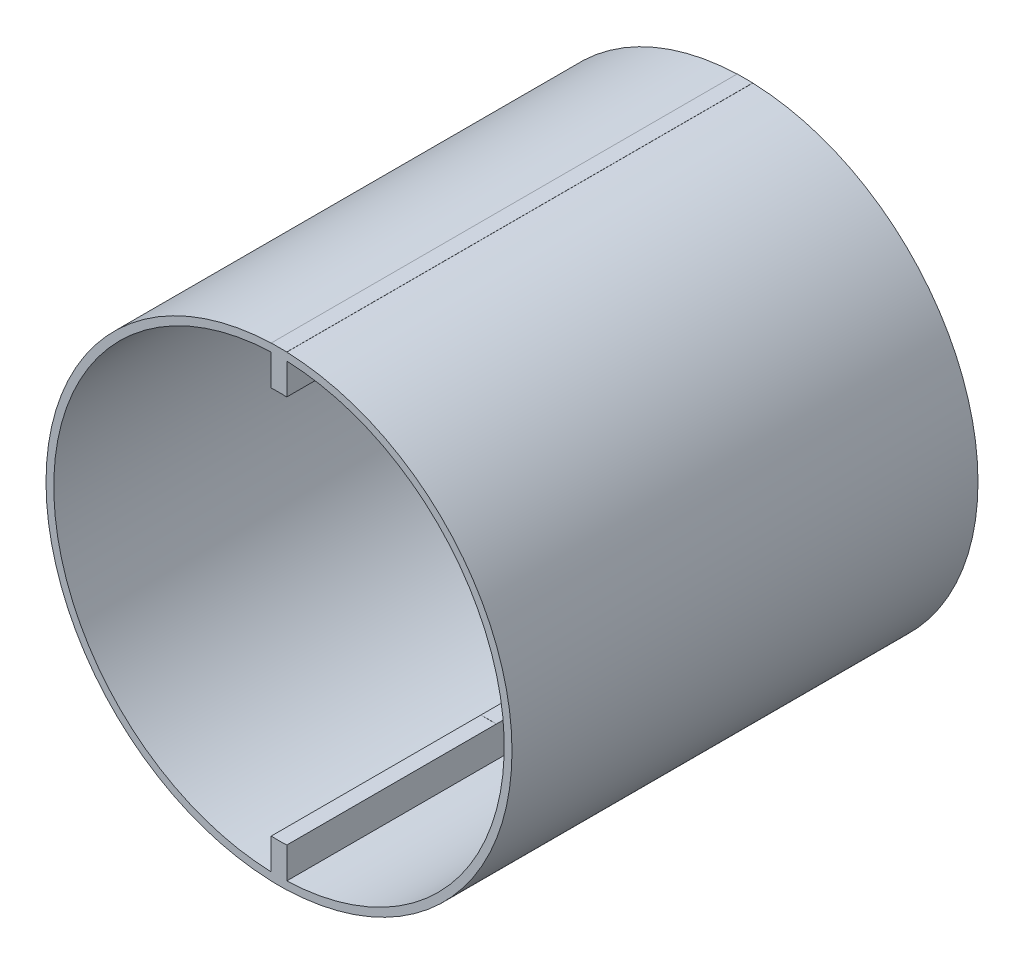
SolidWorks part; units mm, degrees
ref_plane "Plan de face" through (0, 0, 0) normal (0, 0, 1) x (1, 0, 0)
ref_plane "Plan de dessus" through (0, 0, 0) normal (0, 1, 0) x (1, 0, 0)
ref_plane "Plan de droite" through (0, 0, 0) normal (1, 0, 0) x (0, 0, -1)
sketch "Esquisse1" plane through (0, 0, 0) normal (0, 0, 1) x (1, 0, 0)
  line L0 (1, -15.0065) -> (1, -3.3541)
  line L1 (1, 30) -> (-1, 30)
  line L2 (-1, 30) -> (-1, 3.3541)
  line L3 (-1, -30) -> (1, -30)
  line L4 (1, -30) -> (1, -15.0065)
  line L5 (-1, -3.3541) -> (-1, -30)
  line L6 (1, 3.3541) -> (1, 30)
  arc A0 (-1, 3.3541) -> (-1, -3.3541) centre (0, 0) ccw
  arc A1 (1, -3.3541) -> (1, 3.3541) centre (0, 0) ccw
  dimension "D1" = 7
  dimension "D6" = 15.0065
  dimension "D2" = 60
  dimension "D3" = 30
  dimension "D4" = 2
  dimension "D5" = 1
extrude "Boss.-Extru.1" add sketch "Esquisse1" along normal blind 60
sketch "Esquisse2" plane through (0, 0, 60) normal (0, 0, 1) x (1, 0, 0)
  circle A0 centre (0, 0) radius 30
  circle A1 centre (0, 0) radius 29
  dimension "D1" = 60
  dimension "D2" = 58
extrude "Boss.-Extru.2" add sketch "Esquisse2" against normal blind 60
sketch "Esquisse3" plane through (0, 0, 60) normal (0, 0, 1) x (1, 0, 0)
  circle A0 centre (0, 0) radius 25
  dimension "D1" = 50
extrude "Enlèv. mat.-Extru.1" cut sketch "Esquisse3" against normal blind 27
sketch "Esquisse4" plane through (-1, 0, 0) normal (-1, 0, 0) x (0, 0, 1)
sketch "Esquisse5" plane through (-1, 0, 0) normal (-1, 0, 0) x (0, 0, 1)
  line L0 (33, -3.3541) -> (0, -3.3541) construction
  line L1 (33, -24.98) -> (16, -24.98)
  line L2 (33, -24.98) -> (33, -3.3541)
  line L3 (33, -3.3541) -> (16, -3.3541)
  line L4 (16, -24.98) -> (16, -3.3541)
  line L5 (59.4156, 0) -> (-13.0005, 0) construction
  line L6 (33, 3.3541) -> (16, 3.3541)
  line L7 (16, 24.98) -> (16, 3.3541)
  line L8 (33, 24.98) -> (16, 24.98)
  line L9 (33, 24.98) -> (33, 3.3541)
  dimension "D1" = 16
extrude "Enlèv. mat.-Extru.2" cut sketch "Esquisse5" against normal blind 8
sketch "Esquisse6" plane through (0, 0, 33) normal (0, 0, 1) x (1, 0, 0)
  circle A0 centre (0, 0) radius 2.225
  dimension "D1" = 4.45
extrude "Enlèv. mat.-Extru.3" cut sketch "Esquisse6" against normal blind 2
